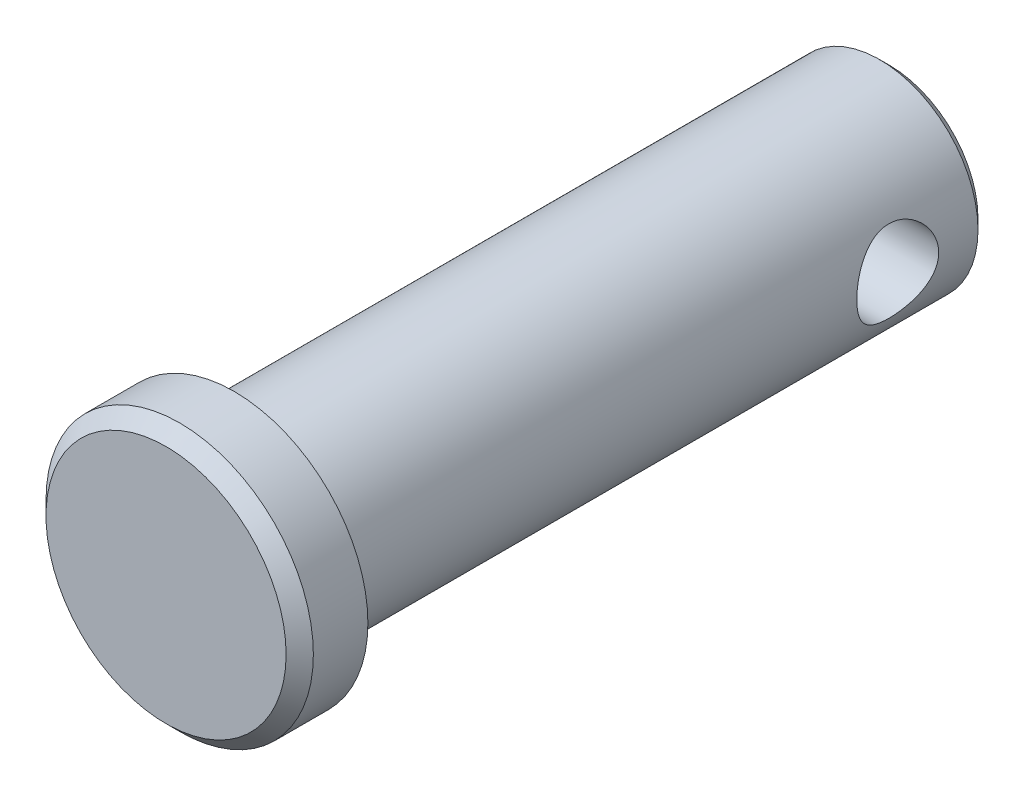
SolidWorks part; units mm, degrees
ref_plane "Front" through (0, 0, 0) normal (0, 0, 1) x (1, 0, 0)
ref_plane "Top" through (0, 0, 0) normal (0, 1, 0) x (1, 0, 0)
ref_plane "Right" through (0, 0, 0) normal (1, 0, 0) x (0, 0, -1)
sketch "Sketch1" plane through (0, 0, 0) normal (0, 0, 1) x (1, 0, 0)
  circle A0 centre (0, 0) radius 4.7625
  point P3 (0, 4.7625)
  point P4 (0, -4.7625)
  dimension "dia" = 9.525
extrude "Extrude1" add sketch "Sketch1" along normal mid plane 31.75
sketch "Sketch2" plane through (0, 0, 15.875) normal (0, 0, 1) x (1, 0, 0)
  circle A0 centre (0, 0) radius 6.477
  dimension "head dia" = 12.954
extrude "Extrude2" add sketch "Sketch2" along normal blind 3.302
chamfer "Chamfer1" distance 0.6604 angle 45 1 edges at (6.477, 0, 19.177)
sketch "Sketch3" plane through (0, 0, 0) normal (1, 0, 0) x (0, 0, -1)
  line L0 (-15.875, -4.7625) -> (-15.875, 4.7625) construction
  circle A0 centre (11.5094, 0) radius 1.9844
  point P2 (9.525, 0)
  dimension "hole dia" = 3.9688
  dimension "useable Lg" = 25.4
extrude "Extrude3" cut sketch "Sketch3" against normal through all and the other way through all
chamfer "Chamfer2" distance 0.4763 angle 45 1 edges at (4.7625, 0, -15.875)
ref_plane "Plane1" through (0, 0, -11.5094) normal (0, 0, 1) x (1, 0, 0)
sketch "Sketch8" plane through (0, 0, 0) normal (1, 0, 0) x (0, 0, -1)
  line L0 (-19.177, 5.8166) -> (-19.177, -5.8166) construction
  line L1 (-18.5166, -6.477) -> (-15.875, -6.477) construction
  line L2 (15.875, -4.2863) -> (15.875, 4.2863) construction
  point P0 (-19.177, 6.477)
  point P1 (-15.875, 6.477)
  point P5 (15.875, 4.7625)
  point P8 (-19.177, -6.477)
  point P9 (15.875, -4.7625)
equation "\"D1@Chamfer1\" = \"head ht@Extrude2\" * .2"
equation "\"D1@Chamfer2\" = \"dia@Sketch1\" * .05"
